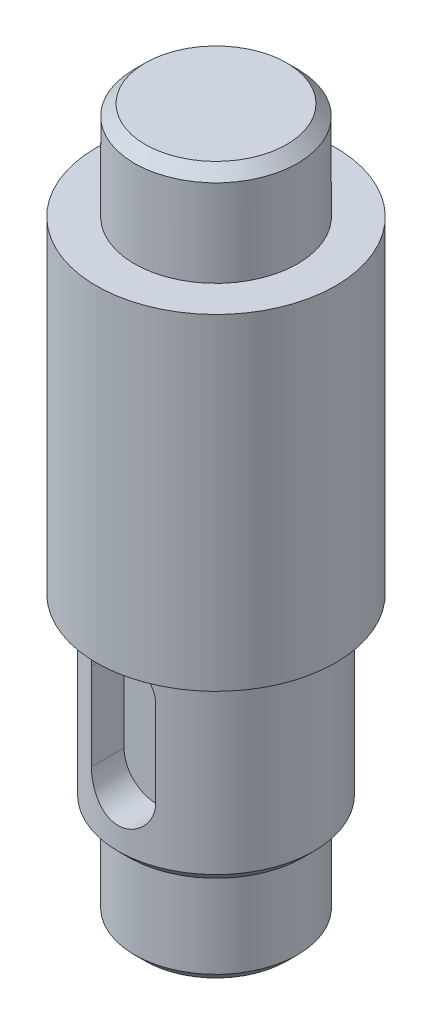
SolidWorks part; units mm, degrees
ref_plane "Front Plane" through (0, 0, 0) normal (0, 0, 1) x (1, 0, 0)
ref_plane "Top Plane" through (0, 0, 0) normal (0, 1, 0) x (1, 0, 0)
ref_plane "Right Plane" through (0, 0, 0) normal (1, 0, 0) x (0, 0, -1)
sketch "Sketch1" plane through (0, 0, 0) normal (0, 0, 1) x (1, 0, 0)
  line L0 (0, 0) -> (0, -60.1423) construction
  line L1 (0, 0) -> (7.5, 0)
  line L2 (7.5, 0) -> (7.5, -9)
  line L3 (7.5, -9) -> (11, -9)
  line L4 (11, -9) -> (11, -39)
  line L5 (11, -39) -> (9, -39)
  line L6 (9, -39) -> (9, -56)
  line L7 (9, -56) -> (7.5, -56)
  line L8 (7.5, -56) -> (7.5, -65)
  line L9 (7.5, -65) -> (0, -65)
  line L10 (0, -60.1423) -> (0, -72.6025) construction
  line L11 (0, -65) -> (0, 0)
  dimension "D1" = 7.5
  dimension "D2" = 9
  dimension "D3" = 30
  dimension "D4" = 3.5
  dimension "D5" = 2
  dimension "D6" = 17
  dimension "D7" = 1.5
  dimension "D8" = 9
revolve "Revolve1" add sketch "Sketch1" angle 360 about L11
chamfer "Chamfer1" distance 1 angle 45 3 edges at (7.5, -65, 0) (9, -56, 0) (7.5, 0, 0)
ref_plane "Plane1" through (0, 0, 9) normal (0, 0, 1) x (1, 0, 0)
sketch "Sketch4" plane through (0, 0, 9) normal (0, 0, 1) x (1, 0, 0)
  line L0 (0, -39) -> (0, -42)
  line L1 (-9, -39) -> (9, -39) construction
  line L2 (0, -42) -> (0, -50) construction
  line L3 (2.9525, -42) -> (2.9525, -50)
  line L4 (-2.9525, -42) -> (-2.9525, -50)
  arc A0 (2.9525, -42) -> (-2.9525, -42) centre (0, -42) ccw
  arc A1 (-2.9525, -50) -> (2.9525, -50) centre (0, -50) ccw
  point P5 (0, -46)
  dimension "D1" = 3
  dimension "D2" = 8
extrude "Cut-Extrude1" cut sketch "Sketch4" against normal blind 3.5
